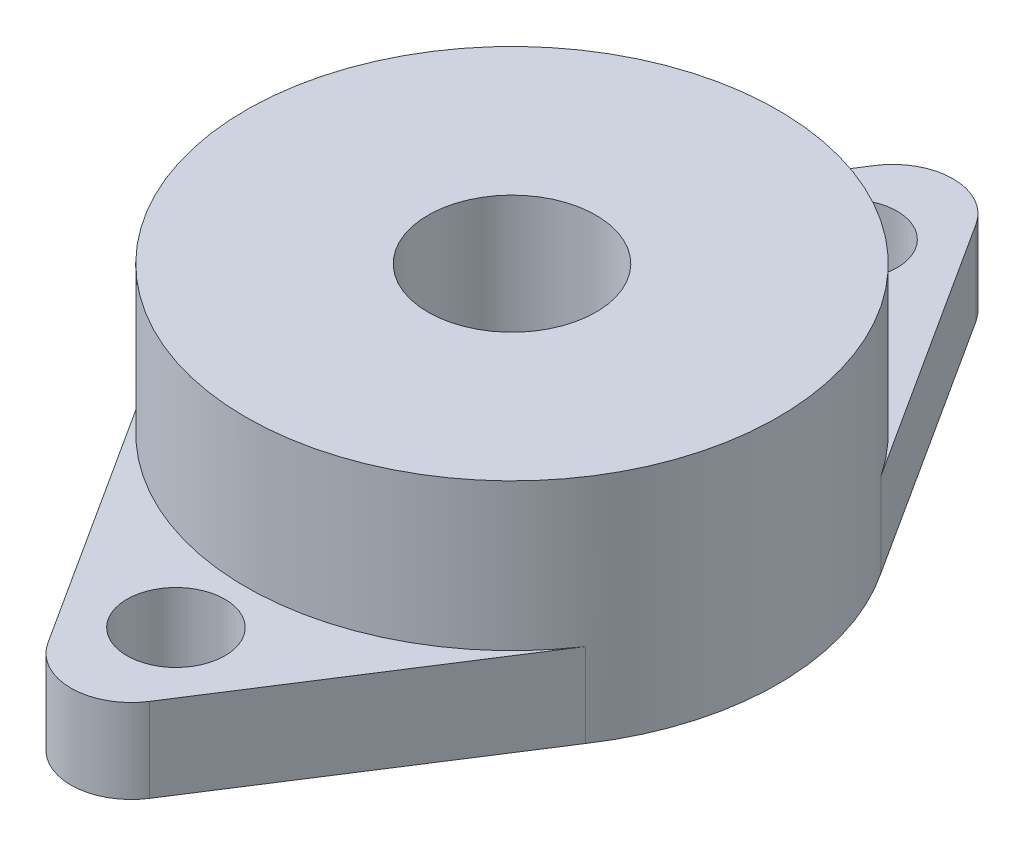
SolidWorks part; units mm, degrees
ref_plane "Front Plane" through (0, 0, 0) normal (0, 0, 1) x (1, 0, 0)
ref_plane "Top Plane" through (0, 0, 0) normal (0, 1, 0) x (1, 0, 0)
ref_plane "Right Plane" through (0, 0, 0) normal (1, 0, 0) x (0, 0, -1)
sketch "Sketch1" plane through (0, 0, 0) normal (0, 1, 0) x (1, 0, 0)
  circle A0 centre (0, 0) radius 19
  dimension "D1" = 38
extrude "Boss-Extrude1" add sketch "Sketch1" along normal blind 16.5
sketch "Sketch2" plane through (0, 0, 0) normal (0, 1, 0) x (1, 0, 0)
  line L0 (0, 31.5) -> (0, -31.5) construction
  line L4 (-15.8019, 10.5498) -> (-3.6195, 29.5227)
  line L5 (15.8019, 10.5498) -> (3.6195, 29.5227)
  line L6 (-15.8019, 10.5498) -> (15.8019, 10.5498)
  circle A1 centre (0, 0) radius 19 construction
  circle A2 centre (0, 27.1986) radius 4.3014
  point P5 (0, 0)
  point P8 (0, 31.5)
  dimension "D1" = 63
extrude "Boss-Extrude2" add sketch "Sketch2" along normal blind 6 contours L0 A2 L4 L6 | A2 L0 L6 L5 | A2 L0 | L0 A2
sketch "Sketch3" plane through (0, 16.5, 0) normal (0, 1, 0) x (1, 0, 0)
  circle A0 centre (0, 0) radius 6
  dimension "D1" = 12
extrude "Cut-Extrude1" cut sketch "Sketch3" against normal through all
sketch "Sketch4" plane through (0, 6, 0) normal (0, 1, 0) x (1, 0, 0)
  line L0 (0, 31.5) -> (0, 0) construction
  arc A0 (3.6195, 29.5227) -> (-3.6195, 29.5227) centre (0, 27.1986) ccw construction
  circle A1 centre (0, 24) radius 3.5
  circle A3 centre (0, 0) radius 19 construction
  dimension "D1" = 24
  dimension "D2" = 7
extrude "Cut-Extrude2" cut sketch "Sketch4" against normal through all
mirror "Mirror1" about plane through (0, 0, 0) normal (0, 0, 1) of "Cut-Extrude2", "Boss-Extrude2"
